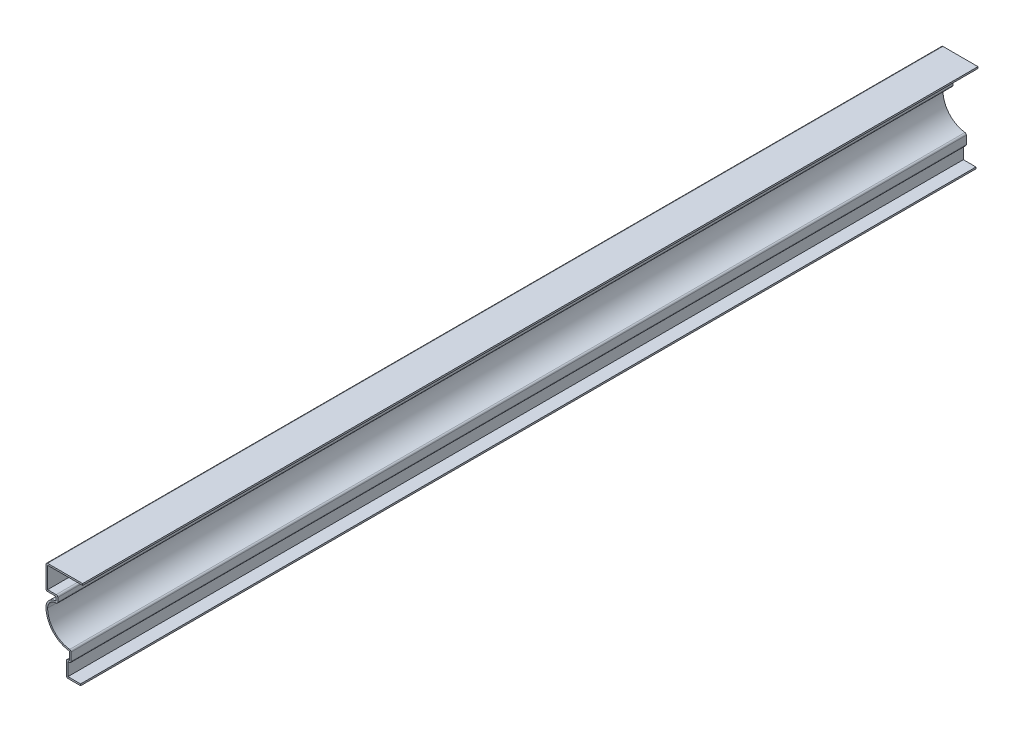
SolidWorks part; units mm, degrees
ref_plane "Front Plane" through (0, 0, 0) normal (0, 0, 1) x (1, 0, 0)
ref_plane "Top Plane" through (0, 0, 0) normal (0, 1, 0) x (1, 0, 0)
ref_plane "Right Plane" through (0, 0, 0) normal (1, 0, 0) x (0, 0, -1)
sketch "Sketch1" plane through (0, 0, 0) normal (0, 0, 1) x (1, 0, 0)
  line L0 (0, 0) -> (-11.1125, 0)
  line L1 (-11.1125, 0) -> (-11.1125, 12.7)
  line L2 (-11.1125, 12.7) -> (-8.7312, 12.7)
  line L3 (-8.7312, 12.7) -> (-8.7312, 19.05)
  line L4 (-19.05, 47.625) -> (-19.05, 50.8)
  line L5 (-19.05, 50.8) -> (-26.9875, 50.8)
  line L6 (-26.9875, 50.8) -> (-26.9875, 69.85)
  line L7 (-26.9875, 69.85) -> (1.5875, 69.85)
  line L8 (-19.05, 47.625) -> (-26.9875, 47.625) construction
  arc A0 (-26.9875, 39.6875) -> (-8.7312, 19.05) centre (-6.1947, 39.6875) ccw
  arc A1 (-26.9875, 39.6875) -> (-19.05, 47.625) centre (-19.05, 39.6875) cw
  point P14 (-26.9875, 47.625)
  dimension "D1" = 11.1125
  dimension "D2" = 12.7
  dimension "D3" = 2.3813
  dimension "D4" = 6.35
  dimension "D5" = 3.175
  dimension "D6" = 28.575
  dimension "D7" = 7.9375
  dimension "D8" = 28.575
  dimension "D9" = 19.05
  dimension "D10" = 15.875
extrude "Extrude-Thin1" add sketch "Sketch1" against normal blind 698.5 thin
fillet "Fillet2" radius 1.27 8 edges at (-11.1125, 0, -349.25) (-11.1125, 12.7, -349.25) (-7.4612, 11.43, -349.25) (-7.4612, 20.2058, -349.25) (-17.78, 46.2329, -349.25) (-17.78, 52.07, -349.25) (-26.9875, 50.8, -349.25) (-26.9875, 69.85, -349.25)
